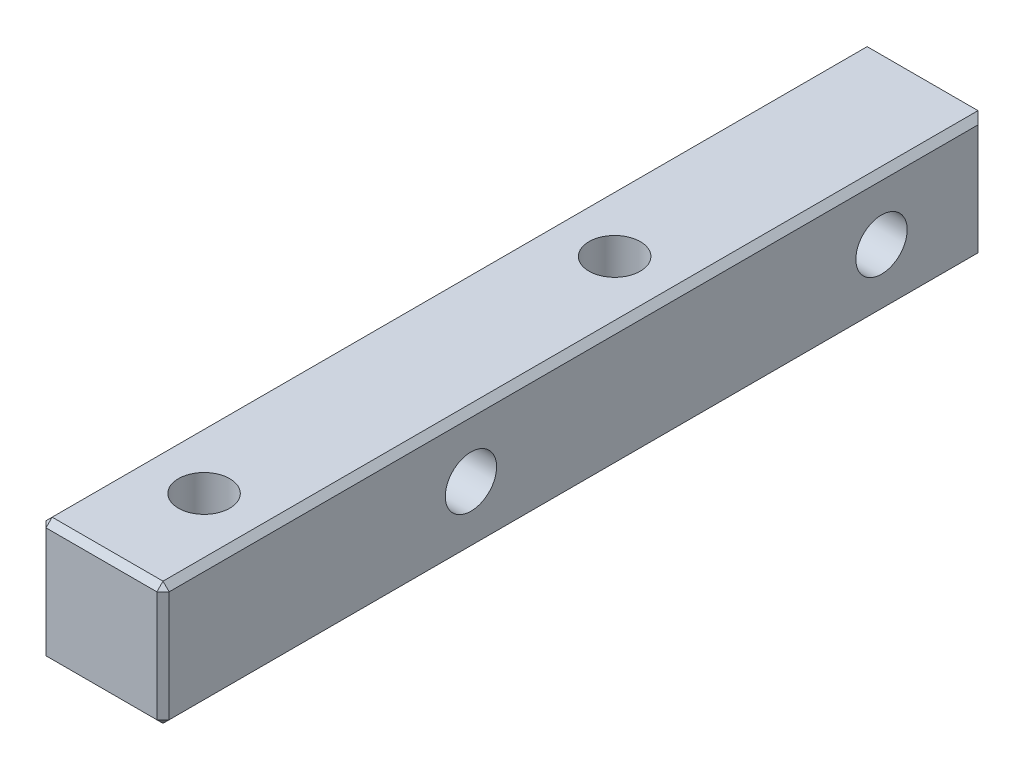
SolidWorks part; units mm, degrees
material "6061 合金"
ref_plane "前视基准面" through (0, 0, 0) normal (0, 0, 1) x (1, 0, 0)
ref_plane "上视基准面" through (0, 0, 0) normal (0, 1, 0) x (1, 0, 0)
ref_plane "右视基准面" through (0, 0, 0) normal (1, 0, 0) x (0, 0, -1)
sketch "草图1" plane through (0, 0, 0) normal (0, 0, 1) x (1, 0, 0)
  line L1 (-3, -3) -> (3, -3)
  line L2 (-3, -3) -> (-3, 3)
  line L3 (-3, 3) -> (3, 3)
  line L4 (3, -3) -> (3, 3)
  line L5 (0, 3) -> (0, -3) construction
  line L6 (-3, 0) -> (3, 0) construction
  point P0 (0, 0)
  dimension "D1" = 6
extrude "凸台-拉伸1" add sketch "草图1" along normal mid plane 40
sketch "草图2" plane through (-3, 0, 0) normal (-1, 0, 0) x (0, 0, 1)
  line L0 (-15, 0) -> (5, 0) construction
  line L1 (-20, 3) -> (-20, -3) construction
  dimension "D1" = 5
  dimension "D2" = 20
sketch "草图3" plane through (0, 3, 0) normal (0, 1, 0) x (1, 0, 0)
  line L0 (0, -15) -> (0, 5) construction
  line L1 (3, -20) -> (-3, -20) construction
  dimension "D1" = 5
  dimension "D2" = 20
hole_wizard " 螺纹孔1" positions "草图4" profile "草图5" tap size "M3" standard "GB" end condition up to next
sketch "草图4" plane through (-3, 0, 0) normal (-1, 0, 0) x (0, 0, 1)
  point P0 (-15, 0)
  point P3 (5, 0)
sketch "草图5" plane through (-3, 0, -15) normal (0, 1, 0) x (0, 0, 1)
  line L0 (0, 0) -> (0, 6)
  line L1 (0, 6) -> (1.25, 6)
  line L2 (1.25, 6) -> (1.25, 0)
  line L5 (1.25, 0) -> (0, 0)
  line L11 (0, -6.35) -> (0, 107.95) construction
  dimension "通孔螺纹孔钻头直径" = 2.5
  dimension "通孔螺纹孔钻头深度" = 6
cosmetic thread "孔螺蚊线1" parameters "D2"=3
cosmetic thread "孔螺蚊线2" parameters "D2"=3
hole_wizard " 螺纹孔2" positions "草图6" profile "草图7" tap size "M3" standard "GB" end condition up to next
sketch "草图6" plane through (0, 3, 0) normal (0, 1, 0) x (1, 0, 0)
  point P0 (0, 5)
  point P3 (0, -15)
sketch "草图7" plane through (0, 3, -5) normal (1, 0, 0) x (0, 0, 1)
  line L0 (0, 0) -> (0, 6)
  line L1 (0, 6) -> (1.25, 6)
  line L2 (1.25, 6) -> (1.25, 0)
  line L5 (1.25, 0) -> (0, 0)
  line L11 (0, -6.35) -> (0, 107.95) construction
  dimension "通孔螺纹孔钻头直径" = 2.5
  dimension "通孔螺纹孔钻头深度" = 6
cosmetic thread "孔螺蚊线3" parameters "D2"=3
cosmetic thread "孔螺蚊线4" parameters "D2"=3
chamfer "倒角1" distance 0.3 angle 45 11 edges at (-3, -3, 0) (3, 0, 20) (3, -3, 0) (0, -3, 20) (0, -3, -20) (-3, 0, -20) (3, 0, -20) (3, 3, 0) (0, 3, 20) (-3, 0, 20) (-3, 3, 0)
